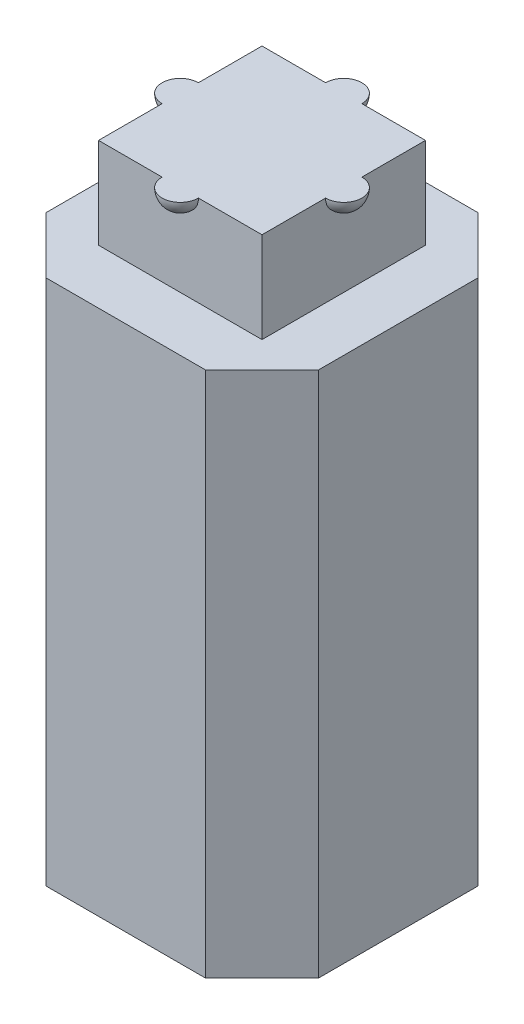
SolidWorks part; units mm, degrees
ref_plane "前视基准面" through (0, 0, 0) normal (0, 0, 1) x (1, 0, 0)
ref_plane "上视基准面" through (0, 0, 0) normal (0, 1, 0) x (1, 0, 0)
ref_plane "右视基准面" through (0, 0, 0) normal (1, 0, 0) x (0, 0, -1)
sketch "草图1" plane through (0, 0, 0) normal (0, 1, 0) x (1, 0, 0)
  line L0 (2.25, -0.4) -> (2.25, -2.25)
  line L1 (-2.25, 2.25) -> (-0.4, 2.25)
  line L2 (-2.25, 2.25) -> (-2.25, 0.4)
  line L3 (-2.25, -2.25) -> (-0.4, -2.25)
  line L4 (2.25, 2.25) -> (2.25, 0.4)
  line L5 (-2.25, -0.4) -> (-2.25, -2.25)
  line L6 (0.4, 2.25) -> (2.25, 2.25)
  line L7 (0.4, -2.25) -> (2.25, -2.25)
  line L8 (2.1897, -3.75) -> (3.75, -2.1897)
  line L17 (3.75, 2.1897) -> (3.75, -2.1897)
  line L18 (2.1897, 3.75) -> (3.75, 2.1897)
  line L19 (2.1897, 3.75) -> (-2.1897, 3.75)
  line L20 (-3.75, 2.1897) -> (-2.1897, 3.75)
  line L21 (-3.75, 2.1897) -> (-3.75, -2.1897)
  line L22 (-3.75, -2.1897) -> (-2.1897, -3.75)
  line L23 (2.1897, -3.75) -> (-2.1897, -3.75)
  arc A0 (0.4, 2.25) -> (-0.4, 2.25) centre (0, 2.25) ccw
  arc A1 (2.25, -0.4) -> (2.25, 0.4) centre (2.25, 0) ccw
  arc A2 (-0.4, -2.25) -> (0.4, -2.25) centre (0, -2.25) ccw
  arc A3 (-2.25, 0.4) -> (-2.25, -0.4) centre (-2.25, 0) ccw
  dimension "D3" = 0.8
  dimension "D4" = 0.8
  dimension "D5" = 0.8
  dimension "D6" = 0.8
extrude "凸台-拉伸1" add sketch "草图1" along normal blind 4
sketch "草图2" plane through (0, 4, 0) normal (0, 1, 0) x (1, 0, 0)
  line L16 (-2.1897, -3.75) -> (2.1897, -3.75)
  line L17 (2.1897, -3.75) -> (3.75, -2.1897)
  line L18 (3.75, -2.1897) -> (3.75, 2.1897)
  line L19 (3.75, 2.1897) -> (2.1897, 3.75)
  line L20 (2.1897, 3.75) -> (-2.1897, 3.75)
  line L21 (-2.1897, 3.75) -> (-3.75, 2.1897)
  line L22 (-3.75, 2.1897) -> (-3.75, -2.1897)
  line L23 (-3.75, -2.1897) -> (-2.1897, -3.75)
  line L24 (-2.1897, -3.75) -> (2.1897, -3.75)
  line L25 (2.1897, -3.75) -> (3.75, -2.1897)
  line L26 (3.75, -2.1897) -> (3.75, 2.1897)
  line L27 (3.75, 2.1897) -> (2.1897, 3.75)
  line L28 (2.1897, 3.75) -> (-2.1897, 3.75)
  line L29 (-2.1897, 3.75) -> (-3.75, 2.1897)
  line L30 (-3.75, 2.1897) -> (-3.75, -2.1897)
  line L31 (-3.75, -2.1897) -> (-2.1897, -3.75)
  dimension "D1" = 0
extrude "凸台-拉伸2" add sketch "草图2" along normal blind 10.5
sketch "草图3" plane through (0, 14.5, 0) normal (0, 1, 0) x (1, 0, 0)
  line L1 (-2.25, 2.25) -> (2.25, 2.25)
  line L2 (-2.25, 2.25) -> (-2.25, -2.25)
  line L3 (-2.25, -2.25) -> (2.25, -2.25)
  line L4 (2.25, 2.25) -> (2.25, -2.25)
  line L5 (-2.25, 2.25) -> (2.25, -2.25) construction
  line L6 (-2.25, -2.25) -> (2.25, 2.25) construction
  point P1 (0, 0)
  dimension "D1" = 4.5
  dimension "D2" = 4.5
extrude "凸台-拉伸3" add sketch "草图3" along normal blind 2.5
sketch "草图4" plane through (0, 17, 0) normal (0, 1, 0) x (1, 0, 0)
  line L0 (2.25, 2.25) -> (-2.25, 2.25) construction
  line L1 (-2.25, -2.25) -> (2.25, -2.25) construction
  line L2 (0, 2.75) -> (0, 1.75)
  line L5 (0, -1.75) -> (0, -2.75)
  arc A0 (0, 2.75) -> (0, 1.75) centre (0, 2.25) ccw
  arc A1 (0, -1.75) -> (0, -2.75) centre (0, -2.25) ccw
  dimension "D1" = 1
  dimension "D2" = 1
revolve "旋转1" add sketch "草图4" angle 360 about L2
sketch "草图5" plane through (0, 17, 0) normal (0, 1, 0) x (1, 0, 0)
  line L0 (-2.25, 2.25) -> (-2.25, -2.25) construction
  line L1 (2.25, -2.25) -> (2.25, 2.25) construction
  line L2 (-2.75, 0) -> (-1.75, 0)
  line L5 (1.75, 0) -> (2.75, 0)
  arc A0 (-2.75, 0) -> (-1.75, 0) centre (-2.25, 0) ccw
  arc A1 (1.75, 0) -> (2.75, 0) centre (2.25, 0) ccw
  dimension "D1" = 1
  dimension "D2" = 1
revolve "旋转2" add sketch "草图5" angle 360 about L2
sketch "草图6" plane through (0, 17, 0) normal (0, 1, 0) x (1, 0, 0)
  line L1 (-2.8177, 2.9698) -> (2.8177, 2.9698)
  line L2 (-2.8177, 2.9698) -> (-2.8177, -2.9698)
  line L3 (-2.8177, -2.9698) -> (2.8177, -2.9698)
  line L4 (2.8177, 2.9698) -> (2.8177, -2.9698)
  line L5 (-2.8177, 2.9698) -> (2.8177, -2.9698) construction
  line L6 (-2.8177, -2.9698) -> (2.8177, 2.9698) construction
  point P0 (0, 0)
extrude "切除-拉伸2" cut sketch "草图6" along normal blind 2.5
